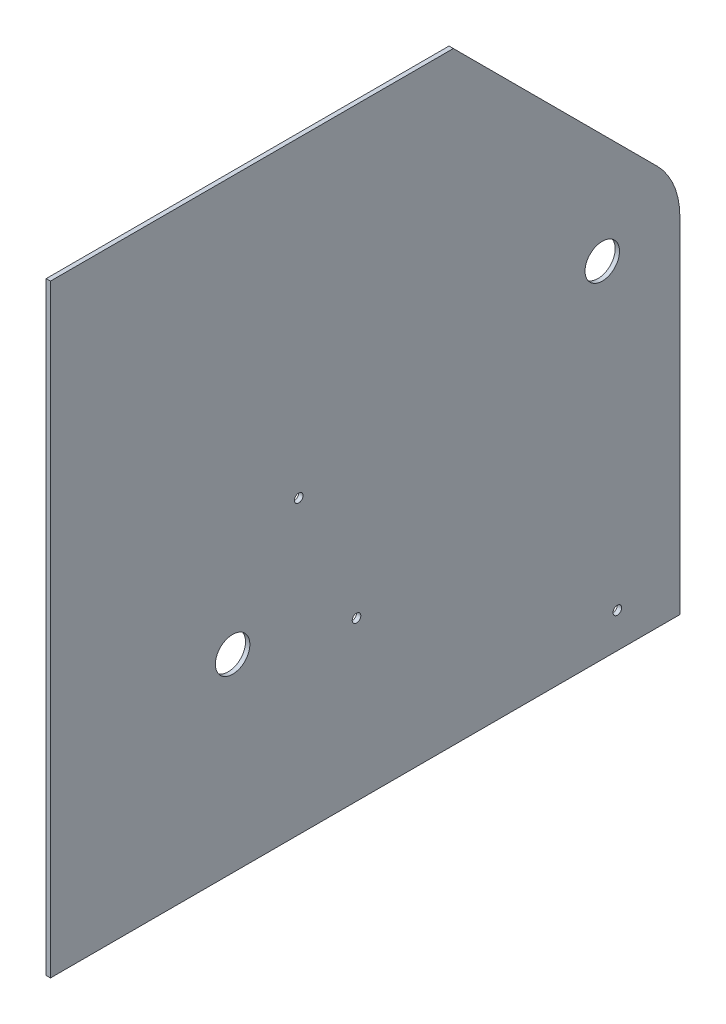
SolidWorks part; units mm, degrees
ref_plane "Front Plane" through (0, 0, 0) normal (0, 0, 1) x (1, 0, 0)
ref_plane "Top Plane" through (0, 0, 0) normal (0, 1, 0) x (1, 0, 0)
ref_plane "Right Plane" through (0, 0, 0) normal (1, 0, 0) x (0, 0, -1)
sketch "Sketch1" plane through (0, 0, 0) normal (1, 0, 0) x (0, 0, -1)
  line L0 (-217.8994, 130.5215) -> (17.5832, 54.3779)
  line L4 (57.15, 0) -> (57.15, -254)
  line L5 (57.15, -254) -> (0, -254)
  arc A0 (-217.8994, 130.5215) -> (0, -254) centre (0, 0) ccw
  circle A1 centre (0, 0) radius 12.7
  arc A2 (57.15, 0) -> (17.5832, 54.3779) centre (0, 0) ccw
  circle A3 centre (0, 0) radius 57.15 construction
  point P18 (0, 0)
  point P29 (0, 0)
  dimension "D1" = 25.4
  dimension "D2" = 254
extrude "Boss-Extrude1" add sketch "Sketch1" along normal blind 3.175
sketch "Sketch2" plane through (3.175, 0, 0) normal (1, 0, 0) x (0, 0, -1)
  circle A0 centre (-180.9898, -137.1562) radius 9.525 construction
  circle A1 centre (-223.5488, -39.2772) radius 9.525 construction
  circle A2 centre (11.1033, -228.1813) radius 9.525 construction
  circle A6 centre (11.1033, -228.1813) radius 3.175
  circle A7 centre (-180.9898, -137.1562) radius 3.175
  circle A8 centre (-223.5488, -39.2772) radius 3.175
  dimension "D1" = 6.35
extrude "Cut-Extrude1" cut sketch "Sketch2" against normal up to next
sketch "Sketch3" plane through (3.175, 0, 0) normal (1, 0, 0) x (0, 0, -1)
  line L0 (0, -254) -> (-254, -254)
  line L1 (-254, 0) -> (-254, -254)
  arc A0 (-217.8994, 130.5215) -> (0, -254) centre (0, 0) ccw construction
  arc A1 (-254, 0) -> (0, -254) centre (0, 0) ccw
extrude "Boss-Extrude2" add sketch "Sketch3" against normal up to surface (3.175 mm away) up to face at (0, -137.1562, 177.8148)
sketch "Sketch4" plane through (3.175, 0, 0) normal (1, 0, 0) x (0, 0, -1)
  line L0 (-254, -254) -> (-406.4, -254)
  line L1 (-406.4, -254) -> (-406.4, 191.4734)
  line L2 (17.5832, 54.3779) -> (-217.8994, 130.5215) construction
  line L3 (-217.8994, 130.5215) -> (-406.4, 191.4734)
  line L4 (-254, 0) -> (-254, -254) construction
  line L5 (-254, 0) -> (-254, -254)
  arc A0 (-217.8994, 130.5215) -> (-254, 0) centre (0, 0) ccw construction
  arc A1 (-217.8994, 130.5215) -> (-254, 0) centre (0, 0) ccw
extrude "Boss-Extrude3" add sketch "Sketch4" against normal up to surface (3.175 mm away) up to face at (0, -137.1562, 177.8148)
sketch "Sketch5" plane through (3.175, 0, 0) normal (1, 0, 0) x (0, 0, -1)
  line L0 (-223.5488, -39.2772) -> (-180.9898, -137.1562) construction
  line L1 (-203.869, -84.5377) -> (-272.2355, -114.6296) construction
  circle A0 centre (-272.2355, -114.6296) radius 12.7
  dimension "D1" = 25.4
extrude "Cut-Extrude2" cut sketch "Sketch5" against normal up to next
sketch "Sketch6" plane through (3.175, 0, 0) normal (1, 0, 0) x (0, 0, -1)
  line L0 (40.4112, 40.4112) -> (-406.4, 487.2223)
  line L1 (57.15, -254) -> (57.15, 0) construction
  line L2 (-406.4, 191.4734) -> (-406.4, 487.2223)
  line L3 (17.5832, 54.3779) -> (-406.4, 191.4734) construction
  line L4 (17.5832, 54.3779) -> (-406.4, 191.4734)
  arc A0 (57.15, 0) -> (17.5832, 54.3779) centre (0, 0) ccw construction
  arc A1 (40.4112, 40.4112) -> (17.5832, 54.3779) centre (0, 0) ccw
  dimension "D1" = 135
extrude "Boss-Extrude4" add sketch "Sketch6" against normal up to surface (3.175 mm away) up to face at (0, -114.6296, 259.5355)
sketch "Sketch7" plane through (3.175, 0, 0) normal (1, 0, 0) x (0, 0, -1)
  line L0 (-406.4, -254) -> (-406.4, 190.5) construction
  line L1 (-406.4, 487.2223) -> (-406.4, -254) construction
  line L3 (-406.4, 190.5) -> (332.9351, 190.5)
  line L4 (-406.4, 190.5) -> (-406.4, 901.5507)
  line L5 (-406.4, 901.5507) -> (332.9351, 901.5507)
  line L6 (332.9351, 190.5) -> (332.9351, 901.5507)
extrude "Cut-Extrude3" cut sketch "Sketch7" against normal up to surface (3.175 mm away) up to face at (0, -114.6296, 259.5355)
